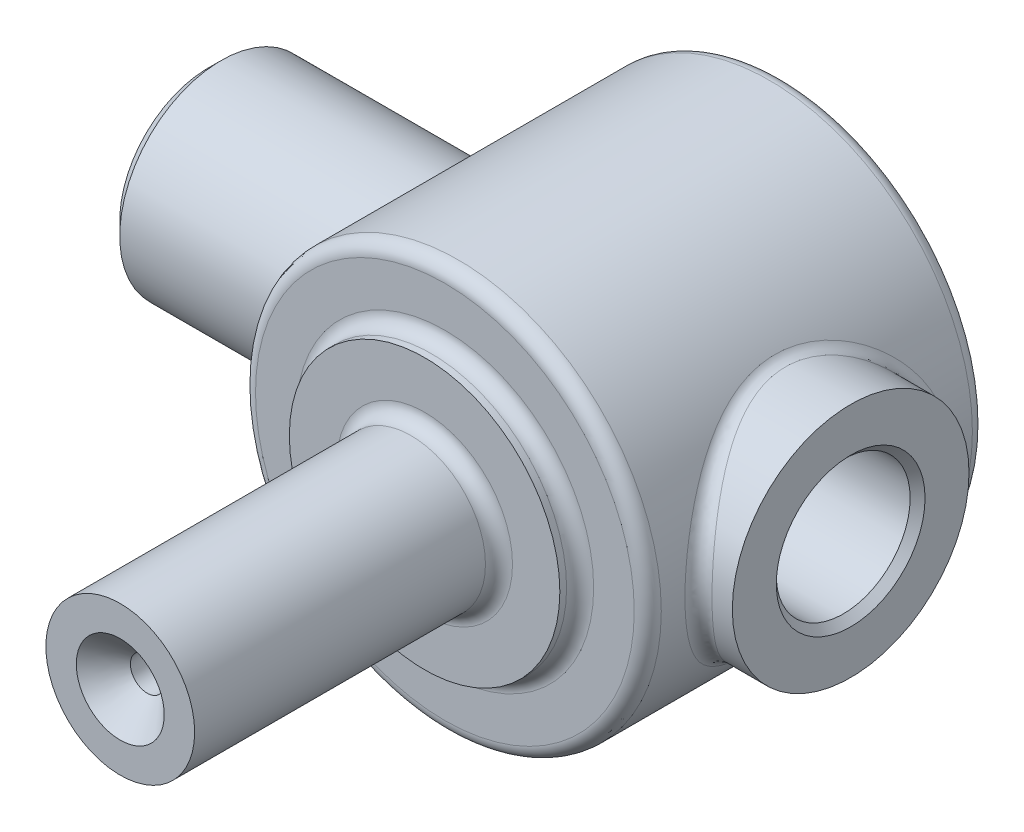
SolidWorks part; units mm, degrees
material "Сталь"
ref_plane "Спереди" through (0, 0, 0) normal (0, 0, 1) x (1, 0, 0)
ref_plane "Сверху" through (0, 0, 0) normal (0, 1, 0) x (1, 0, 0)
ref_plane "Справа" through (0, 0, 0) normal (1, 0, 0) x (0, 0, -1)
sketch "Эскиз1" plane through (0, 0, 0) normal (0, 0, 1) x (1, 0, 0)
  circle A0 centre (0, 0) radius 30
  dimension "D1" = 60
extrude "Бобышка-Вытянуть1" add sketch "Эскиз1" along normal blind 50
sketch "Эскиз2" plane through (0, 0, 50) normal (0, 0, 1) x (1, 0, 0)
  circle A0 centre (0, 0) radius 20
  dimension "D1" = 40
extrude "Бобышка-Вытянуть2" add sketch "Эскиз2" along normal blind 3
sketch "Эскиз3" plane through (0, 0, 53) normal (0, 0, 1) x (1, 0, 0)
  circle A0 centre (0, 0) radius 11
  dimension "D1" = 22
extrude "Бобышка-Вытянуть3" add sketch "Эскиз3" along normal blind 45
sketch "Эскиз4" plane through (0, 0, 0) normal (1, 0, 0) x (0, 0, -1)
  line L0 (0, 0) -> (-50, 0) construction
  line L1 (0, -30) -> (0, 30) construction
  line L2 (-50, 30) -> (-50, -30) construction
  circle A0 centre (-25, 0) radius 17.5
  dimension "D1" = 35
extrude "Бобышка-Вытянуть4" add sketch "Эскиз4" along normal blind 35 and the other way blind 10
sketch "Эскиз8" plane through (0, 0, 0) normal (1, 0, 0) x (0, 0, -1)
  line L0 (0, 0) -> (-50, 0) construction
  line L1 (-50, 30) -> (-50, -30) construction
  circle A0 centre (-25, 0) radius 15
  dimension "D1" = 30
extrude "Бобышка-Вытянуть5" add sketch "Эскиз8" against normal blind 60
cosmetic thread "Условное изображение резьбы2" parameters "D1"=30, "D2"=26.158
sketch "Эскиз5" plane through (0, 0, 0) normal (0, 1, 0) x (1, 0, 0)
  line L0 (-60, -25) -> (35, -25) construction
  line L2 (35, -42.5) -> (35, -7.5) construction
  line L3 (35, -25) -> (35, -34.5)
  line L4 (35, -34.5) -> (-15, -34.5)
  line L5 (-15, -34.5) -> (-15, -32.172)
  line L6 (-15, -32.172) -> (-40, -32.172)
  line L7 (-40, -32.172) -> (-40, -36)
  line L8 (-40, -36) -> (-60, -36)
  line L9 (-60, -36) -> (-60, -25)
  line L10 (-60, -25) -> (35, -25)
  line L11 (-60, -10) -> (-60, -40) construction
  dimension "D1" = 19
  dimension "D2" = 50
  dimension "D3" = 14.344
  dimension "D4" = 25
  dimension "D5" = 22
revolve "Вырез-Повернуть1" cut sketch "Эскиз5" angle 360 about L0
cosmetic thread "Условное изображение резьбы3" parameters "D2"=16
sketch "Эскиз6" plane through (0, 0, 0) normal (0, 1, 0) x (1, 0, 0)
  line L0 (0, -98) -> (0, 0) construction
  line L1 (-11, -98) -> (11, -98) construction
  line L2 (6.5, -98) -> (2.5, -94)
  line L3 (2.5, -94) -> (2.5, -30)
  line L4 (35, -25) -> (-60, -25) construction
  line L5 (35, -34.5) -> (35, -15.5) construction
  line L7 (2.5, -30) -> (0, -30)
  line L8 (6.5, -98) -> (0, -98)
  line L9 (0, -98) -> (0, -30)
  line L10 (-60, -10) -> (-60, -40) construction
  dimension "D1" = 5
  dimension "D2" = 4
  dimension "D3" = 45
  dimension "D4" = 5
revolve "Вырез-Повернуть2" cut sketch "Эскиз6" angle 360 about L9
fillet "Скругление1" radius 2 6 edges at (20, 0, 50) (30, 0, 50) (30, 0, 0) (29.585, 4.9728, 41.7786) (11, 0, 53) (-29.9618, 1.5136, 10.0766)
sketch "Эскиз7" plane through (35, 0, 0) normal (1, 0, 0) x (0, 0, -1)
  circle A0 centre (-25, 0) radius 9.8985
  dimension "D1" = 19.797
extrude "Вырез-Вытянуть1" cut sketch "Эскиз7" against normal up to surface (50 mm away) up to face at (-15, 0, 34.5)
cosmetic thread "Условное изображение резьбы1" parameters "D1"=5, "D2"=22
chamfer "Фаска1" distance 1.1015 angle 45 1 edges at (35, 0, 15.1015)
chamfer "Фаска2" distance 1.921 angle 45 1 edges at (-60, 0, 10)
chamfer "Фаска3" distance 0.828 angle 45 1 edges at (-40, 0, 32.172)
